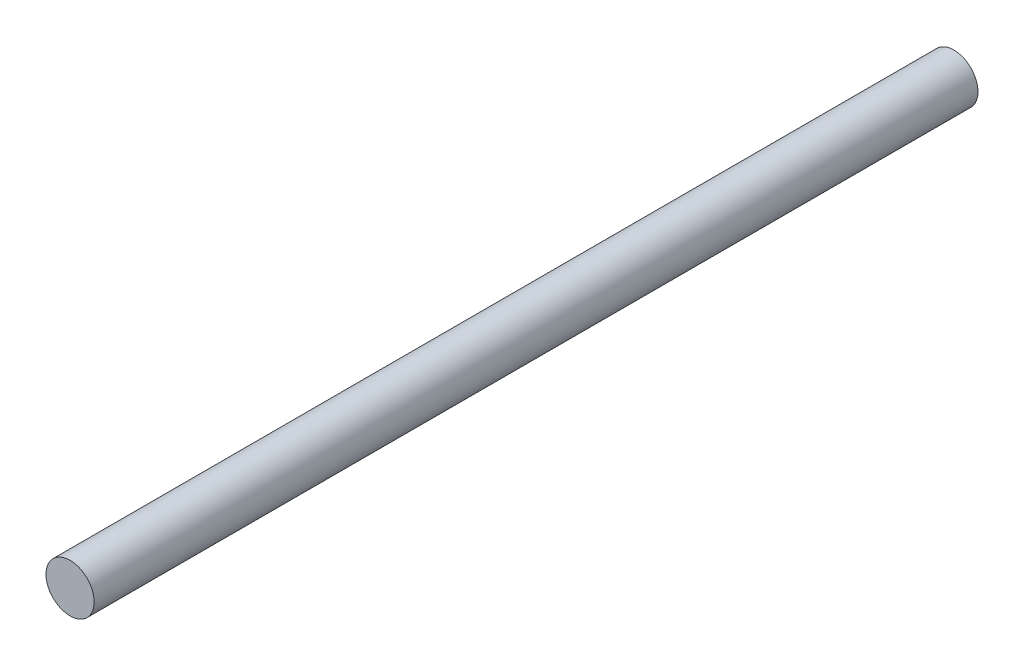
SolidWorks part; units mm, degrees
ref_plane "Front Plane" through (0, 0, 0) normal (0, 0, 1) x (1, 0, 0)
ref_plane "Top Plane" through (0, 0, 0) normal (0, 1, 0) x (1, 0, 0)
ref_plane "Right Plane" through (0, 0, 0) normal (1, 0, 0) x (0, 0, -1)
sketch "Sketch1" plane through (0, 0, 0) normal (0, 0, 1) x (1, 0, 0)
  circle A0 centre (0, 0) radius 3
extrude "Boss-Extrude1" add sketch "Sketch1" along normal blind 110
